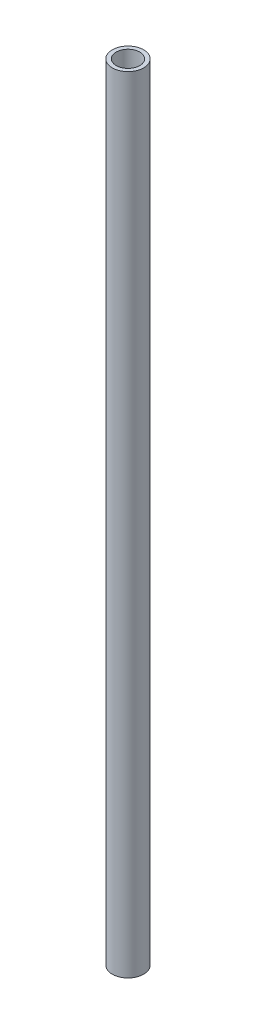
SolidWorks part; units mm, degrees
ref_plane "Спереди" through (0, 0, 0) normal (0, 0, 1) x (1, 0, 0)
ref_plane "Сверху" through (0, 0, 0) normal (0, 1, 0) x (1, 0, 0)
ref_plane "Справа" through (0, 0, 0) normal (1, 0, 0) x (0, 0, -1)
sketch "Эскиз1" plane through (0, 0, 0) normal (0, 1, 0) x (1, 0, 0)
  circle A0 centre (0, 0) radius 4
  circle A1 centre (0, 0) radius 3
extrude "Бобышка-Вытянуть1" add sketch "Эскиз1" along normal blind 200
